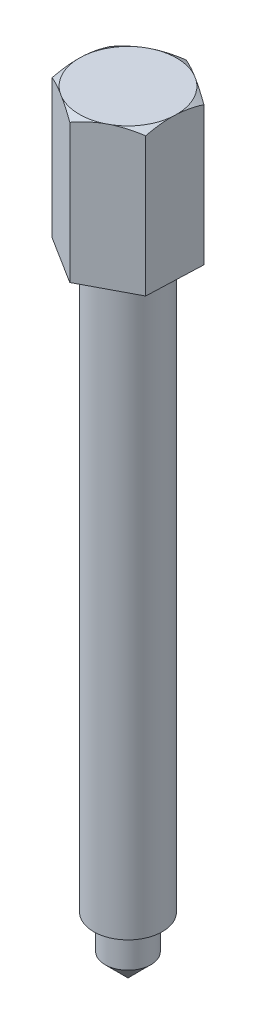
SolidWorks part; units mm, degrees
material "Acero aleado"
ref_plane "Alzado" through (0, 0, 0) normal (0, 0, 1) x (1, 0, 0)
ref_plane "Planta" through (0, 0, 0) normal (0, 1, 0) x (1, 0, 0)
ref_plane "Vista lateral" through (0, 0, 0) normal (1, 0, 0) x (0, 0, -1)
sketch "Croquis1" plane through (0, 0, 0) normal (0, 0, 1) x (1, 0, 0)
  line L0 (0, 0) -> (0, -110)
  line L1 (0, -110) -> (4, -106)
  line L2 (4, -106) -> (4, -100)
  line L3 (4, -100) -> (6, -100)
  line L4 (6, -100) -> (6, 0)
  line L5 (6, 0) -> (0, 0)
  dimension "D1" = 110
  dimension "D2" = 4
  dimension "D3" = 10
  dimension "D4" = 45
  dimension "D5" = 6
revolve "Revolución3" add sketch "Croquis1" angle 360 about L0
cosmetic thread "Rosca cosmética1" parameters "D1"=3.05, "D2"=10.2
sketch "Croquis2" plane through (0, 0, 0) normal (0, 1, 0) x (1, 0, 0)
  line L1 (8.3104, -5.2221) -> (8.6777, 4.586)
  line L2 (8.6777, 4.586) -> (0.3673, 9.8081)
  line L3 (0.3673, 9.8081) -> (-8.3104, 5.2221)
  line L4 (-8.3104, 5.2221) -> (-8.6777, -4.586)
  line L5 (-8.6777, -4.586) -> (-0.3673, -9.8081)
  line L6 (-0.3673, -9.8081) -> (8.3104, -5.2221)
  circle A0 centre (0, 0) radius 8.5 construction
  dimension "D1" = 17
extrude "Saliente-Extruir1" add sketch "Croquis2" along normal blind 25
sketch "Croquis3" plane through (0, 0, 0) normal (1, 0, 0) x (0, 0, -1)
  line L0 (0, 0) -> (0, 27.0022) construction
  line L1 (5.0498, 27.0022) -> (10.2496, 27.0022)
  line L2 (10.2496, 27.0022) -> (10.2496, 24)
  line L3 (10.2496, 24) -> (5.0498, 27.0022)
  line L4 (4.586, 25) -> (9.8081, 25) construction
  dimension "D1" = 1
  dimension "D2" = 30
revolve "Cortar-Revolución1" cut sketch "Croquis3" angle 360 about L0
